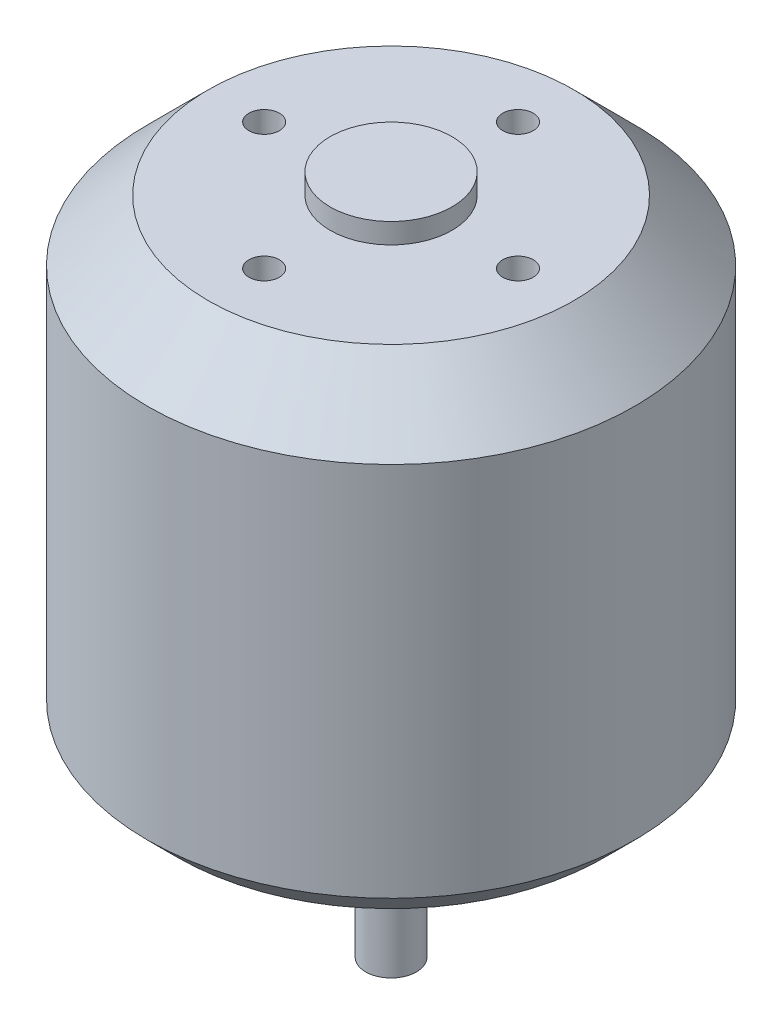
SolidWorks part; units mm, degrees
ref_plane "前视基准面" through (0, 0, 0) normal (0, 0, 1) x (1, 0, 0)
ref_plane "上视基准面" through (0, 0, 0) normal (0, 1, 0) x (1, 0, 0)
ref_plane "右视基准面" through (0, 0, 0) normal (1, 0, 0) x (0, 0, -1)
other "Configuration Table"
sketch "草图1" plane through (0, 0, 0) normal (0, 1, 0) x (1, 0, 0)
  circle A0 centre (0, 0) radius 24
  dimension "D1" = 48
extrude "凸台-拉伸1" add sketch "草图1" along normal blind 46
sketch "草图3" plane through (0, 46, 0) normal (0, 1, 0) x (1, 0, 0)
  circle A0 centre (0, 0) radius 6
  dimension "D1" = 12
extrude "凸台-拉伸2" add sketch "草图3" along normal blind 2
chamfer "倒角1" distance 6 angle 45 1 edges at (0, 46, 24)
chamfer "倒角2" distance 3 angle 45 1 edges at (0, 0, 24)
sketch "草图4" plane through (0, 46, 0) normal (0, -1, 0) x (1, 0, 0)
  circle A0 centre (0, 0) radius 12.5
  circle A1 centre (0, 12.5) radius 1.5
  circle A2 centre (-12.5, 0) radius 1.5
  circle A3 centre (12.5, 0) radius 1.5
  circle A4 centre (0, -12.5) radius 1.5
  dimension "D1" = 25
  dimension "D2" = 3
  dimension "D3" = 3
  dimension "D4" = 3
  dimension "D5" = 3
extrude "切除-拉伸1" cut sketch "草图4" along normal blind 8 contours A2 A0 | A2 A0 | A4 A0 | A4 A0 | A3 | A1
sketch "草图5" plane through (0, 0, 0) normal (0, -1, 0) x (1, 0, 0)
  circle A0 centre (0, 0) radius 8.5
  circle A1 centre (0, 8.5) radius 1.5
  circle A2 centre (8.5, 0) radius 1.5
  circle A3 centre (0, -8.5) radius 1.5
  circle A4 centre (-8.5, 0) radius 1.5
  point P14 (0, 0)
  dimension "D1" = 17
  dimension "D2" = 3
  dimension "D3" = 4
extrude "切除-拉伸2" cut sketch "草图5" against normal blind 8 contours A0 A1 | A0 A2 | A0 A2 | A0 A1 | A0 A4 | A0 A4 | A0 A3 | A0 A3
sketch "草图6" plane through (0, 0, 0) normal (0, -1, 0) x (1, 0, 0)
  circle A0 centre (0, 0) radius 2.5
  dimension "D1" = 5
extrude "凸台-拉伸3" add sketch "草图6" along normal blind 19
